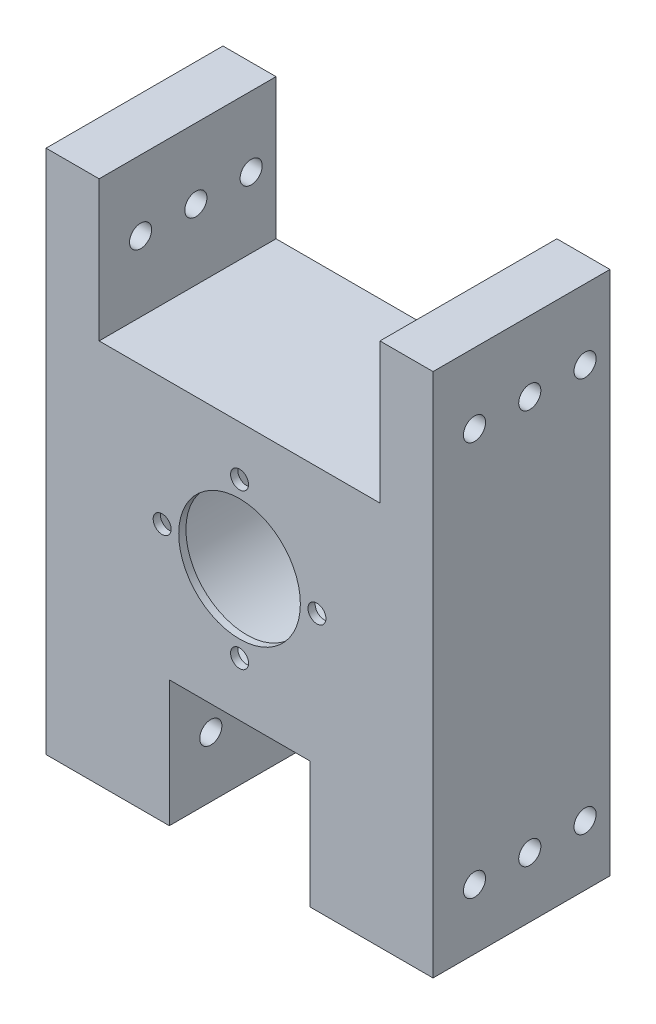
SolidWorks part; units mm, degrees
material "Nylon 6/10"
ref_plane "Front Plane" through (0, 0, 0) normal (0, 0, 1) x (1, 0, 0)
ref_plane "Top Plane" through (0, 0, 0) normal (0, 1, 0) x (1, 0, 0)
ref_plane "Right Plane" through (0, 0, 0) normal (1, 0, 0) x (0, 0, -1)
sketch "Sketch1" plane through (0, 0, 0) normal (0, 0, 1) x (1, 0, 0)
  line L12 (-12.7, -23.74) -> (12.7, -23.74)
  line L13 (-35, -24.5) -> (-35, 48.4)
  line L14 (35, -20) -> (35, 48.4)
  line L22 (-25.4, 48.4) -> (-25.4, 23)
  line L23 (-25.4, 23) -> (25.4, 23)
  line L24 (25.4, 23) -> (25.4, 48.4)
  line L27 (25.4, 48.4) -> (35, 48.4)
  line L28 (-25.4, 48.4) -> (-35, 48.4)
  line L29 (0, 23) -> (0, -23.74) construction
  line L31 (35, -20) -> (35, -46.6)
  line L32 (35, -46.6) -> (12.7, -46.6)
  line L33 (12.7, -23.74) -> (12.7, -46.6)
  line L37 (-35, -24.5) -> (-35, -46.6)
  line L38 (-35, -46.6) -> (-12.7, -46.6)
  line L39 (-12.7, -23.74) -> (-12.7, -46.6)
  circle A0 centre (0, 0) radius 11
  point P9 (0, -11)
  point P17 (0, 11)
  point P20 (0, 23)
  dimension "D4" = 22
  dimension "D1" = 70
  dimension "D2" = 95
  dimension "D3" = 50.8
  dimension "D5" = 25.4
  dimension "D6" = 12
  dimension "D7" = 25.4
  dimension "D8" = 22.86
extrude "Boss-Extrude1" add sketch "Sketch1" along normal blind 55
sketch "Sketch2" plane through (0, 0, 0) normal (0, 0, -1) x (-1, 0, 0)
  circle A0 centre (0, 0) radius 18
  dimension "D1" = 36
extrude "Cut-Extrude1" cut sketch "Sketch2" against normal blind 53.7
sketch "Sketch4" plane through (0, 0, 55) normal (0, 0, 1) x (1, 0, 0)
  circle A0 centre (0, 14) radius 1.625
  circle A1 centre (14, 0) radius 1.625
  circle A2 centre (0, -14) radius 1.625
  circle A3 centre (-14, 0) radius 1.625
  dimension "D1" = 3.25
  dimension "D2" = 14
  dimension "D3" = 14
  dimension "D4" = 14
  dimension "D5" = 14
extrude "Cut-Extrude2" cut sketch "Sketch4" against normal through all
sketch "Sketch5" plane through (0, 0, 0) normal (1, 0, 0) x (0, 0, -1)
  line L0 (-55, 48.4) -> (-55, 23) construction
  line L1 (-55, 35.7) -> (0, 35.7) construction
  line L2 (0, -46.6) -> (0, 48.4) construction
  line L3 (0, 0) -> (-44.7455, 0) construction
  line L4 (-55, -35.7) -> (0, -35.7) construction
  line L5 (-55, -48.4) -> (-55, -23) construction
  line L6 (-45, 35.7) -> (10, 35.7) construction
  line L7 (-35, 35.7) -> (20, 35.7) construction
  line L8 (-55, 35.7) -> (0, 35.7) construction
  line L9 (-45, 35.7) -> (10, 35.7) construction
  line L10 (-65, 35.7) -> (-10, 35.7) construction
  line L11 (-55, 35.7) -> (0, 35.7) construction
  line L12 (-65, 35.7) -> (-10, 35.7) construction
  line L13 (-75, 35.7) -> (-20, 35.7) construction
  line L14 (-75, -35.7) -> (-20, -35.7) construction
  line L15 (-65, -35.7) -> (-10, -35.7) construction
  line L16 (-55, -35.7) -> (0, -35.7) construction
  line L17 (-65, -35.7) -> (-10, -35.7) construction
  line L18 (-45, -35.7) -> (10, -35.7) construction
  line L19 (-55, -35.7) -> (0, -35.7) construction
  line L20 (-35, -35.7) -> (20, -35.7) construction
  line L21 (-45, -35.7) -> (10, -35.7) construction
  line L22 (-55, -35.7) -> (0, -35.7) construction
  line L23 (-55, -48.4) -> (-55, -23) construction
  circle A1 centre (-27.5, 35.7) radius 2
  circle A2 centre (-17.5, 35.7) radius 2
  circle A3 centre (-7.5, 35.7) radius 2
  circle A4 centre (-27.5, 35.7) radius 2
  circle A5 centre (-17.5, 35.7) radius 2
  circle A6 centre (-37.5, 35.7) radius 2
  circle A7 centre (-27.5, 35.7) radius 2
  circle A8 centre (-37.5, 35.7) radius 2
  circle A9 centre (-47.5, 35.7) radius 2
  circle A10 centre (-47.5, -35.7) radius 2
  circle A11 centre (-37.5, -35.7) radius 2
  circle A12 centre (-27.5, -35.7) radius 2
  circle A13 centre (-37.5, -35.7) radius 2
  circle A14 centre (-17.5, -35.7) radius 2
  circle A15 centre (-27.5, -35.7) radius 2
  circle A16 centre (-7.5, -35.7) radius 2
  circle A17 centre (-17.5, -35.7) radius 2
  circle A18 centre (-27.5, -35.7) radius 2
  point P3 (-27.5, 35.7)
  point P9 (-6.2748, 35.7)
  point P10 (-16.7547, 35.7)
  point P11 (-36.3881, 35.7)
  point P12 (-47.266, 35.7)
  point P20 (-47.266, -35.7)
  point P21 (-36.3881, -35.7)
  point P22 (-16.7547, -35.7)
  point P23 (-6.2748, -35.7)
  point P24 (-27.5, -35.7)
  dimension "D1" = 4
  dimension "D2" = 3
  dimension "D3" = 3
extrude "Cut-Extrude3" cut sketch "Sketch5" against normal through all both and the other way through all contours A12 | A14 | A16 | A11 | A10 | A1 | A6 | A9 | A2 | A3
sketch "Sketch6" plane through (35, 0, 0) normal (1, 0, 0) x (0, 0, -1)
  line L2 (-23, -1.1) -> (-23, 51.2858)
  line L3 (-23, 51.2858) -> (26.64, 51.2858)
  line L4 (26.64, 51.2858) -> (26.64, -56.9941)
  line L5 (26.64, -56.9941) -> (-23, -56.9941)
  line L6 (-23, -56.9941) -> (-23, -1.1)
extrude "Cut-Extrude4" cut sketch "Sketch6" against normal blind 74
